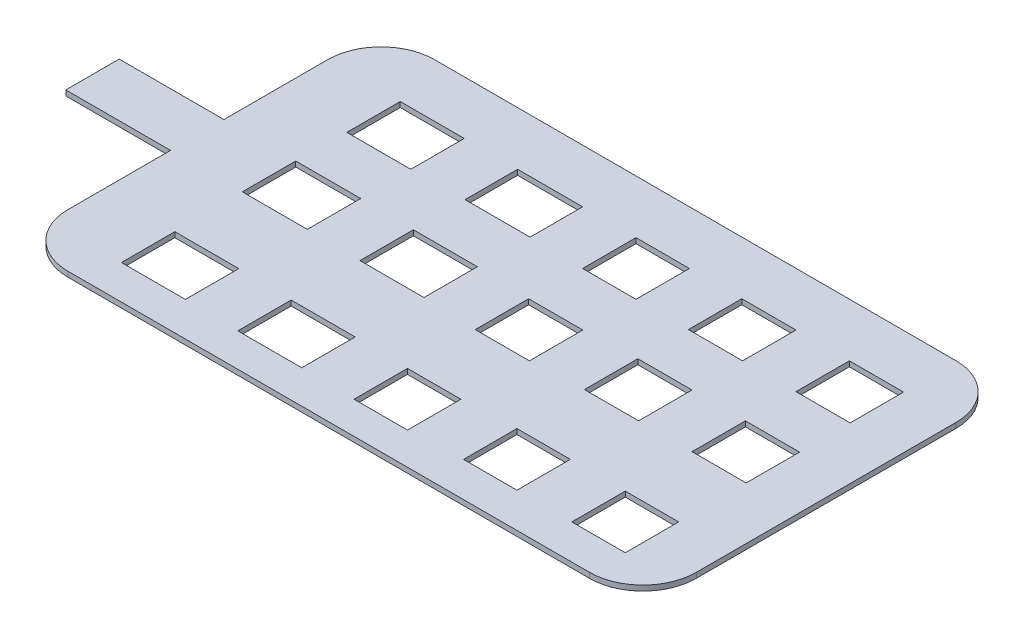
SolidWorks part; units mm, degrees
ref_plane "Front Plane" through (0, 0, 0) normal (0, 0, 1) x (1, 0, 0)
ref_plane "Top Plane" through (0, 0, 0) normal (0, 1, 0) x (1, 0, 0)
ref_plane "Right Plane" through (0, 0, 0) normal (1, 0, 0) x (0, 0, -1)
sketch "Sketch5" plane through (0, 0, 0) normal (0, 1, 0) x (1, 0, 0)
  line L1 (-2.4682, -1.7373) -> (2.5118, -1.7373)
  line L2 (-2.9782, -1.2273) -> (-2.9782, -0.2482)
  line L3 (-2.4682, 1.7627) -> (2.5118, 1.7627)
  line L4 (3.0218, -1.2273) -> (3.0218, 1.2527)
  line L5 (-2.9782, -1.7373) -> (-2.2854, -1.3332) construction
  line L6 (0.476, 0.2348) -> (0.476, -0.2752)
  line L7 (1.7484, -1.7373) -> (1.7484, -1.75)
  line L8 (0.0218, 1.7627) -> (0.0218, 0.0127) construction
  line L9 (-2.2854, 0.7427) -> (-1.6746, 0.7427)
  line L10 (-2.2854, 0.7427) -> (-2.2854, 1.2527)
  line L11 (-2.2854, 1.2527) -> (-1.6746, 1.2527)
  line L12 (-1.6746, 0.7427) -> (-1.6746, 1.2527)
  line L13 (-2.2854, 0.7427) -> (-1.6746, 1.2527) construction
  line L14 (-2.2854, 1.2527) -> (-1.6746, 0.7427) construction
  line L23 (-2.2854, -0.9) -> (-1.6746, -0.9)
  line L24 (-1.6746, -0.9) -> (-1.6746, -1.41)
  line L25 (-2.2854, -1.41) -> (-1.6746, -1.41)
  line L26 (-2.2854, -0.9) -> (-2.2854, -1.41)
  line L28 (-2.2926, -0.2482) -> (-1.672, -0.2482)
  line L29 (-2.2926, -0.2482) -> (-2.2926, 0.2618)
  line L30 (-2.2926, 0.2618) -> (-1.672, 0.2618)
  line L31 (-1.672, -0.2482) -> (-1.672, 0.2618)
  line L32 (-1.162, -0.2553) -> (-0.5511, -0.2553)
  line L33 (-1.162, -0.2553) -> (-1.162, 0.2547)
  line L34 (-1.162, 0.2547) -> (-0.5511, 0.2547)
  line L35 (-0.5511, -0.2553) -> (-0.5511, 0.2547)
  line L40 (-1.98, 0.9977) -> (1.4934, 0.9977) construction
  line L41 (-1.1646, 0.7507) -> (-0.544, 0.7507)
  line L42 (-1.1646, 0.7507) -> (-1.1646, 1.2527)
  line L43 (-1.1646, 1.2527) -> (-0.544, 1.2527)
  line L44 (-0.544, 0.7507) -> (-0.544, 1.2527)
  line L45 (-1.98, -1.155) -> (1.7181, -1.155) construction
  line L46 (-1.1646, -1.4196) -> (-0.5537, -1.4196)
  line L47 (-1.1646, -1.4196) -> (-1.1646, -0.9096)
  line L48 (-1.1646, -0.9096) -> (-0.5537, -0.9096)
  line L49 (-0.5537, -1.4196) -> (-0.5537, -0.9096)
  line L50 (-3.9782, 0.2618) -> (-2.9782, 0.2618)
  line L51 (-2.9782, -0.2482) -> (-3.9782, -0.2482)
  line L52 (-0.0411, -0.2752) -> (0.476, -0.2752)
  line L53 (-0.0411, -0.2752) -> (-0.0411, 0.2348)
  line L54 (-0.0411, 0.2348) -> (0.476, 0.2348)
  line L56 (-0.034, 0.7427) -> (0.476, 0.7427)
  line L57 (-0.034, 0.7427) -> (-0.034, 1.2527)
  line L58 (-0.034, 1.2527) -> (0.476, 1.2527)
  line L59 (0.476, 0.7427) -> (0.476, 1.2527)
  line L60 (-0.0437, -1.4298) -> (0.4663, -1.4298)
  line L61 (-0.0437, -1.4298) -> (-0.0437, -0.9198)
  line L62 (-0.0437, -0.9198) -> (0.4663, -0.9198)
  line L63 (0.4663, -1.4298) -> (0.4663, -0.9198)
  line L76 (-3.9782, 0.2618) -> (-3.9782, -0.2482)
  line L77 (-2.9782, 0.2618) -> (-2.9782, 1.2527)
  line L78 (2.5206, -1.4045) -> (2.5206, -0.8945)
  line L79 (2.5206, -0.8945) -> (2.0106, -0.8945)
  line L80 (0.0218, -0.2752) -> (0.0218, -1.7373) construction
  line L81 (2.0106, -1.4045) -> (2.0106, -0.8945)
  line L82 (1.4934, 0.2601) -> (1.4934, -0.2499)
  line L83 (0.9763, -0.2499) -> (1.4934, -0.2499)
  line L84 (0.9763, -0.2499) -> (0.9763, 0.2601)
  line L85 (0.9763, 0.2601) -> (1.4934, 0.2601)
  line L86 (0.9763, 0.7427) -> (1.4934, 0.7427)
  line L87 (0.9763, 0.7427) -> (0.9763, 1.2527)
  line L88 (0.9763, 1.2527) -> (1.4934, 1.2527)
  line L89 (1.4934, 0.7427) -> (1.4934, 1.2527)
  line L90 (0.9763, -1.4045) -> (1.4863, -1.4045)
  line L91 (0.9763, -1.4045) -> (0.9763, -0.8945)
  line L92 (0.9763, -0.8945) -> (1.4863, -0.8945)
  line L93 (1.4863, -1.4045) -> (1.4863, -0.8945)
  line L94 (2.5206, -1.4045) -> (2.0106, -1.4045)
  line L95 (2.5206, 0.2601) -> (2.0034, 0.2601)
  line L96 (2.5206, -0.2499) -> (2.5206, 0.2601)
  line L97 (2.5206, -0.2499) -> (2.0034, -0.2499)
  line L98 (2.0034, 0.2601) -> (2.0034, -0.2499)
  line L99 (2.5206, 0.7427) -> (2.5206, 1.2527)
  line L100 (2.5206, 1.2527) -> (2.0034, 1.2527)
  line L101 (2.0034, 0.7427) -> (2.0034, 1.2527)
  line L102 (2.5206, 0.7427) -> (2.0034, 0.7427)
  arc A0 (-2.4682, -1.7373) -> (-2.9782, -1.2273) centre (-2.4682, -1.2273) cw
  arc A1 (2.5118, -1.7373) -> (3.0218, -1.2273) centre (2.5118, -1.2273) ccw
  arc A2 (2.5118, 1.7627) -> (3.0218, 1.2527) centre (2.5118, 1.2527) cw
  arc A3 (-2.9782, 1.2527) -> (-2.4682, 1.7627) centre (-2.4682, 1.2527) cw
  point P0 (0, 0)
  point P7 (-0.0437, -1.1748)
  point P10 (-1.98, 0.9977)
  point P17 (1.2348, 1.2527)
  point P59 (-1.1646, 1.0017)
  point P88 (3.0218, -1.7373)
  point P92 (3.0218, 1.7627)
  point P96 (-2.9782, 1.7627)
  dimension "D15" = 0.51
  dimension "D1" = 6
  dimension "D2" = 3.5
  dimension "D3" = 0.51
  dimension "D4" = 0.51
  dimension "D5" = 1
  dimension "D6" = 1
  dimension "D7" = 0.51
  dimension "D8" = 0.51
  dimension "D9" = 0.51
  dimension "D10" = 0.51
  dimension "D11" = 0.51
  dimension "D12" = 0.51
  dimension "D13" = 0.51
  dimension "D14" = 0.6108
  dimension "D16" = 0.51
  dimension "D17" = 0.51
  dimension "D18" = 0.51
  dimension "D19" = 0.51
  dimension "D20" = 0.51
  dimension "D21" = 0.51
extrude "Boss-Extrude1" add sketch "Sketch5" along normal blind 0.05 contours A3 L77 L50 L76 L51 L2 A0 L1 A1 L4 A2 L3 L98 L95 L96 L97 L93 L90 L91 L92 L89 L86 L87 L88 L63 L60 L61 L62 L59 L56 L57 L58 L49 L46 L47 L48 L44 L41 L42 L43 L35 L32
